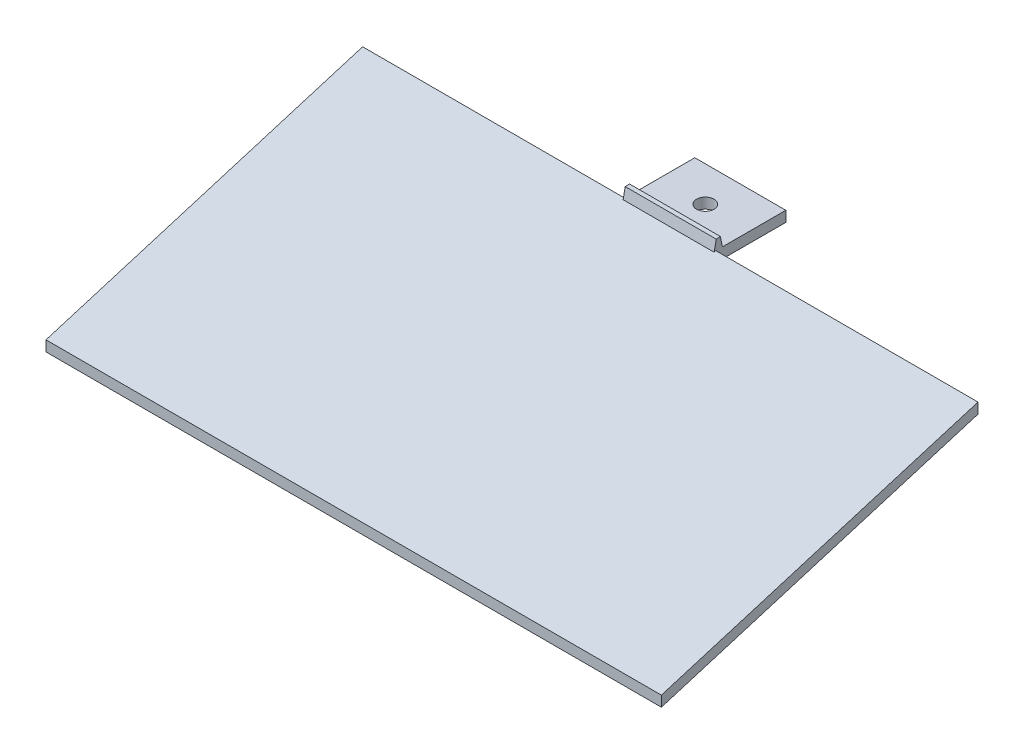
SolidWorks part; units mm, degrees
ref_plane "Alzado" through (0, 0, 0) normal (0, 0, 1) x (1, 0, 0)
ref_plane "Planta" through (0, 0, 0) normal (0, 1, 0) x (1, 0, 0)
ref_plane "Vista lateral" through (0, 0, 0) normal (1, 0, 0) x (0, 0, -1)
sketch "Croquis2" plane through (0, 0, 0) normal (1, 0, 0) x (0, 0, -1)
  line L0 (0, 0) -> (-90.45, 0)
  line L1 (0, 0) -> (0, 27.28)
  line L2 (-90.45, 0) -> (0, 27.28)
  line L3 (-90.45, 0) -> (-90.45, 3)
  line L4 (0, 27.28) -> (0, 30.28)
  line L5 (0, 30.28) -> (-90.45, 3)
  dimension "D1" = 90.45
  dimension "D2" = 27.28
  dimension "D3" = 3
  dimension "D4" = 3
extrude "Saliente-Extruir1" add sketch "Croquis2" along normal blind 175.8 contours L4 L5 L3 L2
sketch "Croquis3" plane through (175.8, 0, 0) normal (1, 0, 0) x (0, 0, -1)
  line L0 (0, 27.28) -> (20, 27.28)
  line L1 (20, 27.28) -> (20, 30.28)
  line L2 (20, 30.28) -> (0, 30.28)
  line L3 (0, 30.28) -> (0, 27.28)
  dimension "D1" = 20
extrude "Saliente-Extruir2" add sketch "Croquis3" against normal up to vertex (175.8 mm away)
sketch "Croquis4" plane through (0, 30.28, 0) normal (0, 1, 0) x (1, 0, 0)
  line L2 (0, 20) -> (175.8, 20) construction
  line L3 (100.9, 20) -> (175.8, 20)
  line L4 (100.9, 0) -> (74.9, 0)
  line L5 (100.9, 0) -> (100.9, 20)
  line L6 (100.9, 20) -> (74.9, 20)
  line L7 (74.9, 0) -> (74.9, 20)
  line L8 (100.9, 20) -> (100.9, 0)
  line L9 (100.9, 0) -> (175.8, 0)
  line L10 (175.8, 20) -> (175.8, 0)
  line L11 (74.9, 20) -> (0, 20)
  line L12 (74.9, 20) -> (74.9, 0)
  line L13 (74.9, 0) -> (0, 0)
  line L14 (0, 20) -> (0, 0)
  circle A0 centre (87.9, 10) radius 2.5
  point P6 (87.9, 10)
  line M5 (175.8, 0) -> (175.8, 20)
  line M6 (175.8, 20) -> (0, 20)
  line M7 (0, 20) -> (0, 0)
  line M8 (0, 0) -> (175.8, 0)
  dimension "D2" = 5
  dimension "D1" = 26
extrude "Cortar-Extruir1" cut sketch "Croquis4" against normal blind 165.8 contours L5 M8 M5 M6 | L7 M8 M6 M7 | A0
sketch "Croquis5" plane through (100.9, 0, 0) normal (1, 0, 0) x (0, 0, -1)
  line L5 (1.8784, 30.28) -> (0.7459, 36.0004)
  line L6 (0, 30.28) -> (20, 30.28) construction
  line L7 (0.7459, 36.0004) -> (-0.5556, 29.7982)
  line L8 (-0.5556, 29.7982) -> (1.8784, 30.28)
extrude "Saliente-Extruir3" add sketch "Croquis5" against normal up to vertex
sketch "Croquis6" plane through (100.9, 0, 0) normal (1, 0, 0) x (0, 0, -1)
  line L0 (0.1304, 33.067) -> (1.3121, 33.1402)
  line L1 (0.7459, 36.0004) -> (-0.4852, 30.1337) construction
  line L2 (1.8784, 30.28) -> (0.7459, 36.0004) construction
  line L3 (1.3121, 33.1402) -> (0.7459, 36.0004)
  line L4 (0.7459, 36.0004) -> (0.1304, 33.067)
extrude "Cortar-Extruir2" cut sketch "Croquis6" against normal up to vertex (26 mm away)
